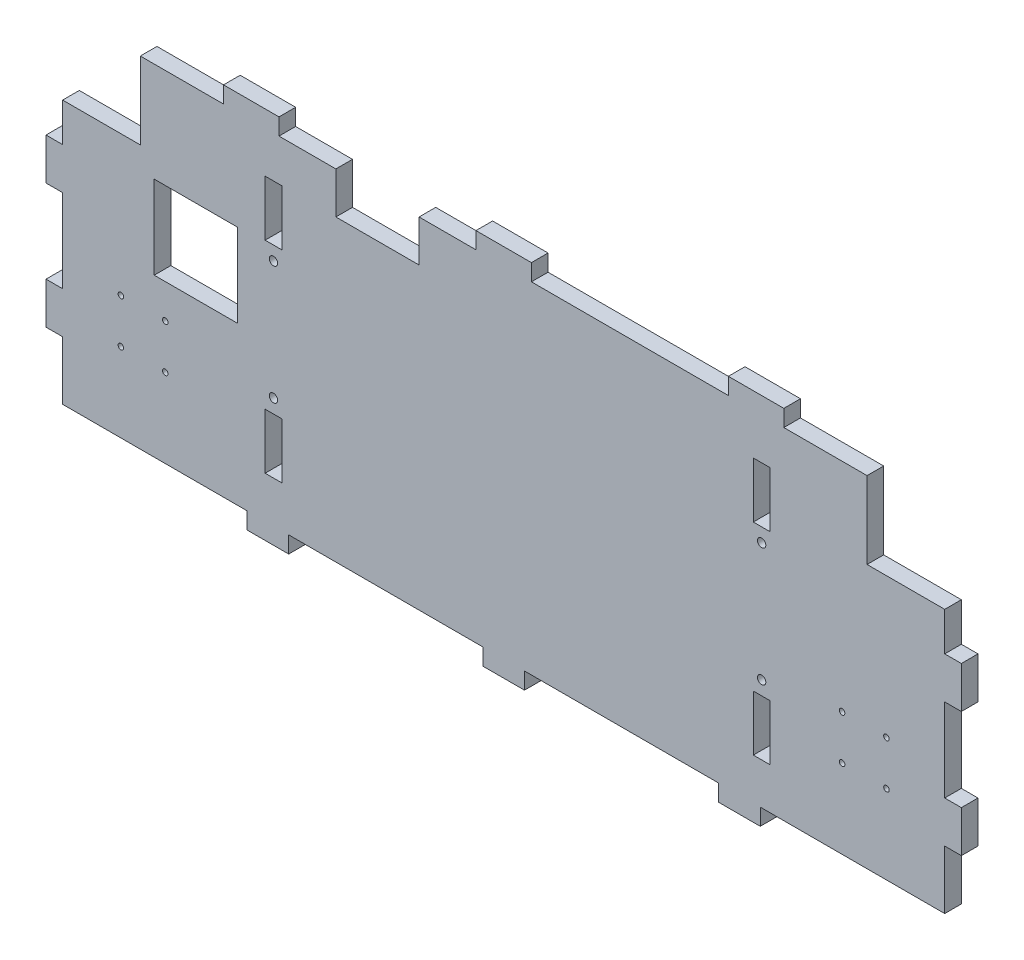
SolidWorks part; units mm, degrees
ref_plane "Plan de face" through (0, 0, 0) normal (0, 0, 1) x (1, 0, 0)
ref_plane "Plan de dessus" through (0, 0, 0) normal (0, 1, 0) x (1, 0, 0)
ref_plane "Plan de droite" through (0, 0, 0) normal (1, 0, 0) x (0, 0, -1)
sketch "Esquisse1" plane through (0, 0, 0) normal (0, 0, 1) x (1, 0, 0)
  line L0 (-159, 35) -> (-131, 35)
  line L1 (0, 102.0551) -> (0, -193.4247) construction
  line L2 (-159, 35) -> (-159, -60)
  line L3 (-159, -60) -> (159, -60)
  line L4 (159, 35) -> (159, -60)
  line L6 (131, 35) -> (131, 62.75)
  line L7 (131, 62.75) -> (-131, 62.75)
  line L8 (-131, 35) -> (-131, 62.75)
  line L9 (159, 35) -> (131, 35)
  line L10 (96, 47.75) -> (90, 47.75)
  line L11 (96, 47.75) -> (96, 27.75)
  line L12 (96, 27.75) -> (90, 27.75)
  line L13 (90, 47.75) -> (90, 27.75)
  line L14 (96, -25.01) -> (90, -25.01)
  line L15 (96, -25.01) -> (96, -45.01)
  line L16 (96, -45.01) -> (90, -45.01)
  line L17 (90, -25.01) -> (90, -45.01)
  line L18 (-80, 47.75) -> (-86, 47.75)
  line L19 (-80, 47.75) -> (-80, 27.75)
  line L20 (-80, 27.75) -> (-86, 27.75)
  line L21 (-86, 47.75) -> (-86, 27.75)
  line L22 (-80, -25.01) -> (-86, -25.01)
  line L23 (-80, -25.01) -> (-80, -45.01)
  line L24 (-80, -45.01) -> (-86, -45.01)
  line L25 (-86, -25.01) -> (-86, -45.01)
  line L26 (-95.9865, 26.8256) -> (-125.9865, 26.8256)
  line L27 (-95.9865, 26.8256) -> (-95.9865, -3.1744)
  line L28 (-95.9865, -3.1744) -> (-125.9865, -3.1744)
  line L29 (-125.9865, 26.8256) -> (-125.9865, -3.1744)
  dimension "D1" = 95
  dimension "D2" = 28
  dimension "D3" = 28
  dimension "D4" = 95
  dimension "D6" = 262
  dimension "D7" = 122.75
  dimension "D5" = 159
  dimension "D8" = 318
  dimension "D9" = 6
  dimension "D10" = 20
  dimension "D11" = 20
  dimension "D12" = 6
  dimension "D13" = 6
  dimension "D14" = 20
  dimension "D15" = 6
  dimension "D16" = 20
  dimension "D17" = 52.76
  dimension "D18" = 63
  dimension "D19" = 73
  dimension "D20" = 73
  dimension "D21" = 52.76
  dimension "D22" = 15
  dimension "D23" = 15
  dimension "D24" = 63
  dimension "D25" = 30
  dimension "D26" = 30
extrude "Boss.-Extru.1" add sketch "Esquisse1" along normal blind 6
sketch "Esquisse2" plane through (0, 0, 6) normal (0, 0, 1) x (1, 0, 0)
  line L0 (-159, -60) -> (159, -60) construction
  line L1 (-92.5, -60) -> (-77.5, -60)
  line L2 (-92.5, -60) -> (-92.5, -66)
  line L3 (-92.5, -66) -> (-77.5, -66)
  line L4 (-77.5, -60) -> (-77.5, -66)
  line L5 (-159, 35) -> (-159, -60) construction
  line L6 (-7.5, -60) -> (7.5, -60)
  line L7 (-7.5, -60) -> (-7.5, -66)
  line L8 (-7.5, -66) -> (7.5, -66)
  line L9 (7.5, -60) -> (7.5, -66)
  line L10 (77.5, -60) -> (92.5, -60)
  line L11 (77.5, -60) -> (77.5, -66)
  line L12 (77.5, -66) -> (92.5, -66)
  line L13 (92.5, -60) -> (92.5, -66)
  line L14 (176.2958, 0) -> (-249.7093, -3.2925) construction
  line L15 (0, 107.6082) -> (0, -117.4775) construction
  line L16 (-131, 35) -> (-159, 35) construction
  line L17 (-159, 21.09) -> (-165, 21.09)
  line L18 (-159, 21.09) -> (-159, 6.09)
  line L19 (-159, 6.09) -> (-165, 6.09)
  line L20 (-165, 21.09) -> (-165, 6.09)
  line L21 (-159, -23.91) -> (-165, -23.91)
  line L22 (-159, -23.91) -> (-159, -38.91)
  line L23 (-159, -38.91) -> (-165, -38.91)
  line L24 (-165, -23.91) -> (-165, -38.91)
  line L25 (165, -23.91) -> (165, -38.91)
  line L26 (159, -38.91) -> (165, -38.91)
  line L27 (159, -23.91) -> (159, -38.91)
  line L28 (159, -23.91) -> (165, -23.91)
  line L29 (165, 21.09) -> (165, 6.09)
  line L30 (159, 6.09) -> (165, 6.09)
  line L31 (159, 21.09) -> (159, 6.09)
  line L32 (159, 21.09) -> (165, 21.09)
  line L33 (131, 62.75) -> (-131, 62.75) construction
  line L34 (101, 62.75) -> (81, 62.75)
  line L35 (101, 62.75) -> (101, 68.75)
  line L36 (101, 68.75) -> (81, 68.75)
  line L37 (81, 62.75) -> (81, 68.75)
  line L38 (-131, 62.75) -> (-131, 35) construction
  line L39 (-81, 62.75) -> (-101, 62.75)
  line L40 (-81, 62.75) -> (-81, 68.75)
  line L41 (-81, 68.75) -> (-101, 68.75)
  line L42 (-101, 62.75) -> (-101, 68.75)
  line L43 (10, 62.75) -> (-10, 62.75)
  line L44 (10, 62.75) -> (10, 68.75)
  line L45 (10, 68.75) -> (-10, 68.75)
  line L46 (-10, 62.75) -> (-10, 68.75)
  line L47 (131, 35) -> (131, 62.75) construction
  dimension "D1" = 66.5
  dimension "D2" = 70
  dimension "D3" = 15
  dimension "D4" = 15
  dimension "D5" = 70
  dimension "D6" = 15
  dimension "D7" = 6
  dimension "D8" = 6
  dimension "D9" = 6
  dimension "D10" = 6
  dimension "D11" = 13.91
  dimension "D12" = 15
  dimension "D13" = 30
  dimension "D14" = 15
  dimension "D15" = 20
  dimension "D16" = 20
  dimension "D17" = 20
  dimension "D18" = 30
  dimension "D19" = 30
  dimension "D20" = 121
  dimension "D21" = 6
  dimension "D22" = 6
  dimension "D23" = 6
  dimension "D24" = 6
extrude "Boss.-Extru.2" add sketch "Esquisse2" against normal blind 6
sketch "Esquisse3" plane through (0, 0, 0) normal (0, 0, -1) x (-1, 0, 0)
  line L2 (0, 141.59) -> (0, -167.3887) construction
  line L3 (83, 57.185) -> (83, -52.5738) construction
  line L4 (-93, 52.3657) -> (-93, -53.0892) construction
  line L5 (-90, 27.75) -> (-96, 27.75) construction
  line L6 (-96, 27.75) -> (-96, 47.75) construction
  line L7 (-96, -25.01) -> (-90, -25.01) construction
  line L8 (80, -25.01) -> (86, -25.01) construction
  line L9 (80, -45.01) -> (80, -25.01) construction
  line L10 (86, 27.75) -> (80, 27.75) construction
  line L11 (159, 6.09) -> (159, -23.91) construction
  line L12 (122, -15.49) -> (138, -15.49) construction
  line L13 (122, -15.49) -> (122, -31.49) construction
  line L14 (122, -31.49) -> (138, -31.49) construction
  line L15 (138, -15.49) -> (138, -31.49) construction
  line L16 (159, -60) -> (92.5, -60) construction
  circle A0 centre (138, -31.49) radius 1
  circle A1 centre (138, -15.49) radius 1
  circle A2 centre (122, -15.49) radius 1
  circle A3 centre (122, -31.49) radius 1
  circle A4 centre (-122, -31.49) radius 1
  circle A5 centre (-122, -15.49) radius 1
  circle A6 centre (-138, -15.49) radius 1
  circle A7 centre (-138, -31.49) radius 1
  circle A9 centre (83, 22.75) radius 1.5
  circle A10 centre (83, -20.01) radius 1.5
  circle A13 centre (-93, 22.75) radius 1.5
  circle A14 centre (-93, -20.01) radius 1.5
  dimension "D7" = 2
  dimension "D8" = 2
  dimension "D9" = 2
  dimension "D10" = 2
  dimension "D11" = 3
  dimension "D12" = 3
  dimension "D13" = 3
  dimension "D14" = 3
  dimension "D17" = 5
  dimension "D18" = 5
  dimension "D20" = 5
  dimension "D3" = 16
  dimension "D4" = 21
  dimension "D5" = 28.51
  dimension "D15" = 5
  dimension "D16" = 3
  dimension "D19" = 3
extrude "Enlèv. mat.-Extru.1" cut sketch "Esquisse3" against normal blind 6
sketch "Esquisse4" plane through (0, 0, 0) normal (0, 0, -1) x (-1, 0, 0)
  line L0 (10, 62.75) -> (81, 62.75) construction
  line L1 (30.5, 62.75) -> (60.5, 62.75)
  line L2 (30.5, 62.75) -> (30.5, 47.75)
  line L3 (30.5, 47.75) -> (60.5, 47.75)
  line L4 (60.5, 62.75) -> (60.5, 47.75)
  line L5 (10, 68.75) -> (10, 62.75) construction
  dimension "D1" = 20.5
  dimension "D2" = 30
  dimension "D3" = 15
extrude "Enlèv. mat.-Extru.2" cut sketch "Esquisse4" against normal blind 6
equation "\"D5@Esquisse1\"=\"D8@Esquisse1\"/2"
